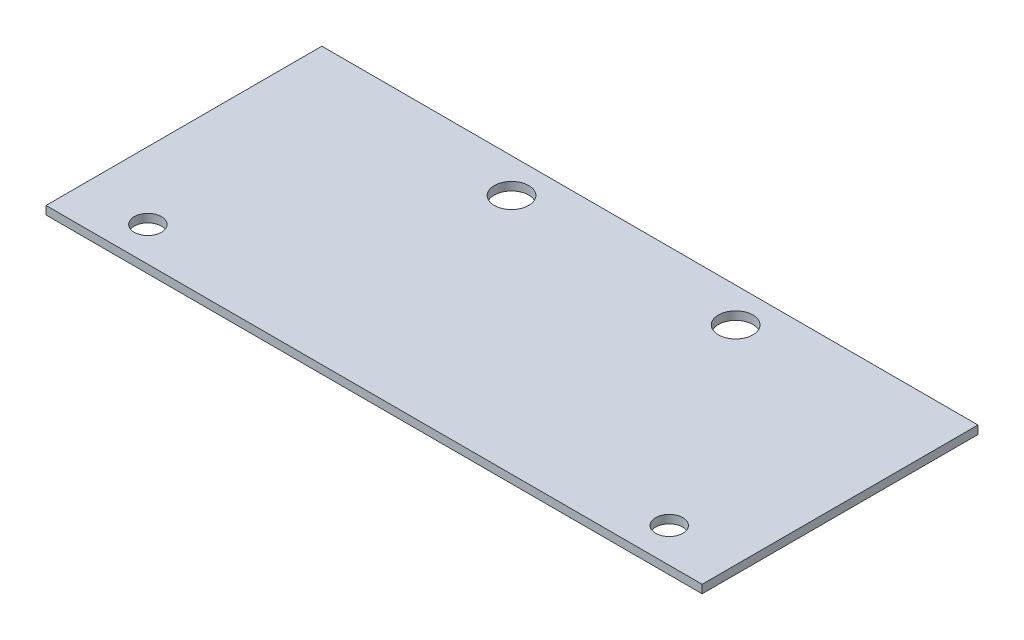
SolidWorks part; units mm, degrees
ref_plane "Front Plane" through (0, 0, 0) normal (0, 0, 1) x (1, 0, 0)
ref_plane "Top Plane" through (0, 0, 0) normal (0, 1, 0) x (1, 0, 0)
ref_plane "Right Plane" through (0, 0, 0) normal (1, 0, 0) x (0, 0, -1)
sketch "Sketch1" plane through (0, 0, 0) normal (0, 1, 0) x (1, 0, 0)
  line L0 (-50.2216, -9.3191) -> (70.6062, -9.3191)
  line L1 (70.6062, -9.3191) -> (70.6062, 41.4809)
  line L2 (70.6062, 41.4809) -> (35.6304, 41.4809)
  line L3 (35.6304, 41.4809) -> (-15.1696, 41.4809)
  line L4 (-15.1696, 41.4809) -> (-50.2216, 41.4809)
  line L5 (-50.2216, 41.4809) -> (-50.2216, -9.3191)
  dimension "D1" = 50.8
  dimension "D2" = 120.8278
  dimension "D3" = 50.8
  dimension "D4" = 35.052
  dimension "D5" = 50.8
  dimension "D6" = 50.8
extrude "Boss-Extrude1" add sketch "Sketch1" along normal blind 1.524
sketch "Sketch2" plane through (0, 1.524, 0) normal (0, 1, 0) x (1, 0, 0)
  line L0 (-50.2216, 41.4809) -> (-50.2216, -9.3191) construction
  line L1 (70.6062, 41.4809) -> (-50.2216, 41.4809) construction
  line L2 (70.6062, 41.4809) -> (-50.2216, 41.4809) construction
  line L3 (-50.2216, 41.4809) -> (-50.2216, -9.3191) construction
  circle A0 centre (-37.8137, -2.9691) radius 2.5019
  circle A1 centre (58.1983, -2.9691) radius 2.5019
  circle A2 centre (32.3284, 35.1309) radius 3.175
  circle A3 centre (-8.9466, 35.1309) radius 3.175
  point P18 (-50.8656, 37.3139)
  dimension "D3" = 5.0038
  dimension "D4" = 5.0038
  dimension "D7" = 6.35
  dimension "D8" = 6.35
  dimension "D1" = 96.012
  dimension "D2" = 44.45
  dimension "D5" = 12.4079
  dimension "D6" = 41.275
  dimension "D9" = 44.45
  dimension "D10" = 6.35
  dimension "D11" = 6.35
  dimension "D12" = 41.275
extrude "Cut-Extrude1" cut sketch "Sketch2" against normal through all
